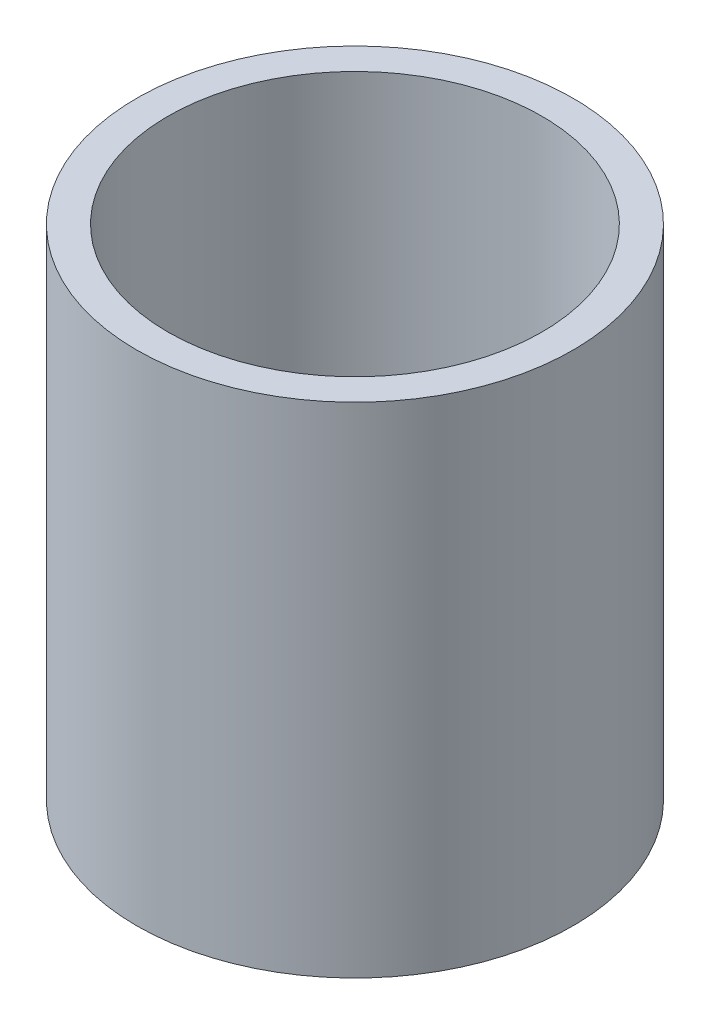
SolidWorks part; units mm, degrees
ref_plane "Front Plane" through (0, 0, 0) normal (0, 0, 1) x (1, 0, 0)
ref_plane "Top Plane" through (0, 0, 0) normal (0, 1, 0) x (1, 0, 0)
ref_plane "Right Plane" through (0, 0, 0) normal (1, 0, 0) x (0, 0, -1)
sketch "Sketch1" plane through (0, 0, 0) normal (0, 1, 0) x (1, 0, 0)
  circle A0 centre (0, 0) radius 3
  circle A1 centre (0, 0) radius 3.5
  dimension "D1" = 6
  dimension "D2" = 7
extrude "Boss-Extrude1" add sketch "Sketch1" along normal blind 8
